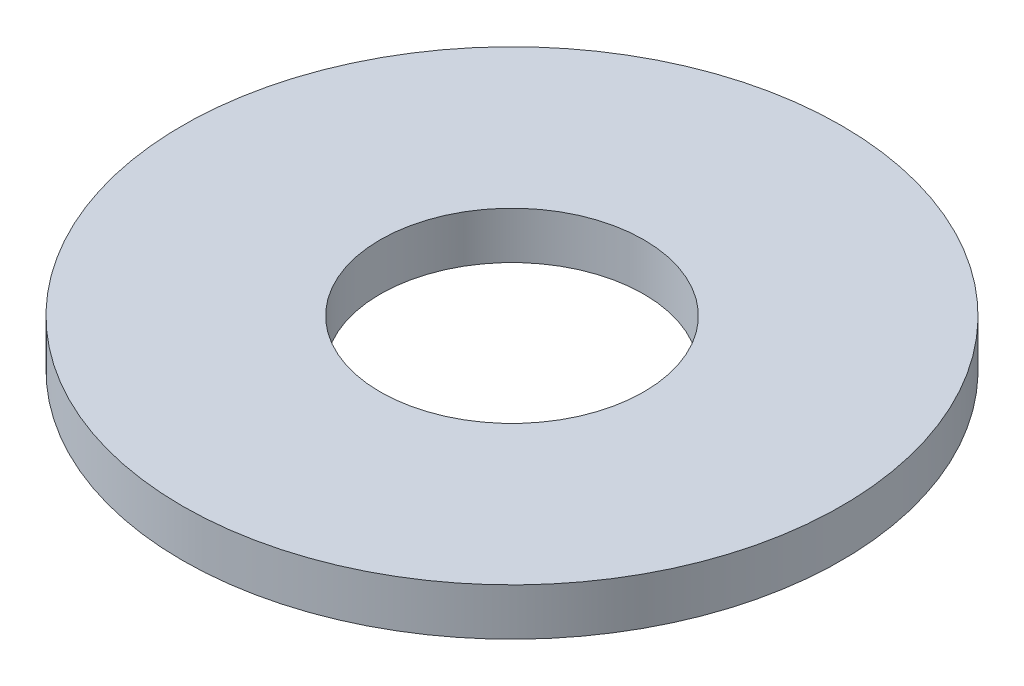
SolidWorks part; units mm, degrees
material "Acier allié"
ref_plane "Plan de face" through (0, 0, 0) normal (0, 0, 1) x (1, 0, 0)
ref_plane "Plan de dessus" through (0, 0, 0) normal (0, 1, 0) x (1, 0, 0)
ref_plane "Plan de droite" through (0, 0, 0) normal (1, 0, 0) x (0, 0, -1)
sketch "Esquisse1" plane through (0, 0, 0) normal (0, 1, 0) x (1, 0, 0)
  circle A0 centre (0, 0) radius 3.5
  circle A1 centre (0, 0) radius 1.4
  dimension "D1" = 7
  dimension "D2" = 2.8
extrude "Boss.-Extru.1" add sketch "Esquisse1" along normal blind 0.5
